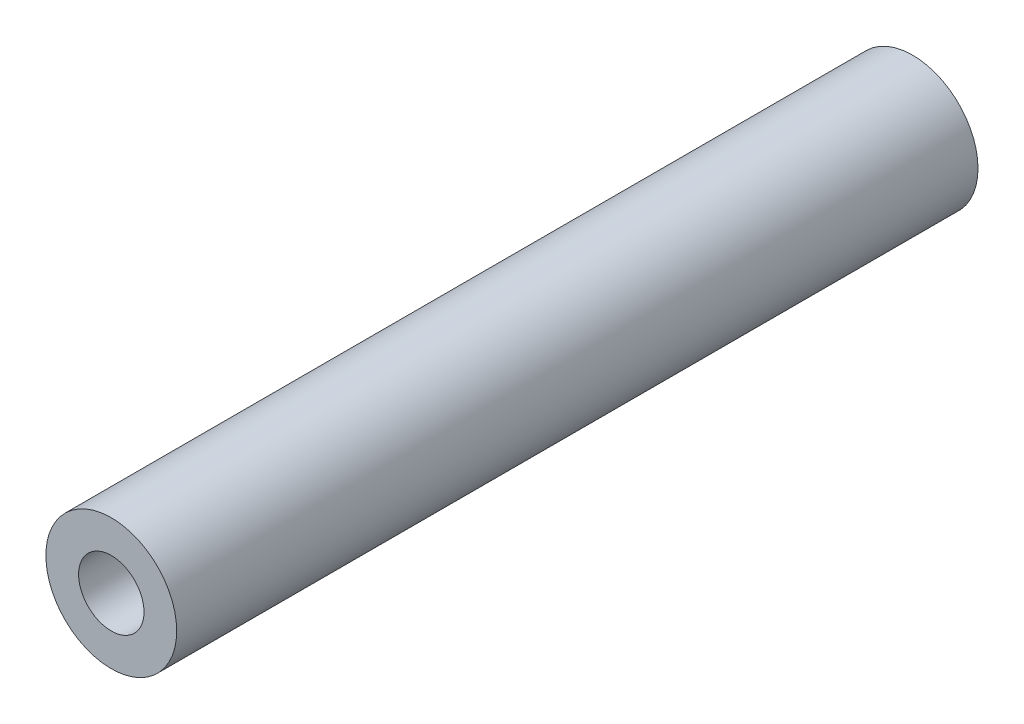
SolidWorks part; units mm, degrees
ref_plane "Plan de face" through (0, 0, 0) normal (0, 0, 1) x (1, 0, 0)
ref_plane "Plan de dessus" through (0, 0, 0) normal (0, 1, 0) x (1, 0, 0)
ref_plane "Plan de droite" through (0, 0, 0) normal (1, 0, 0) x (0, 0, -1)
sketch "Esquisse1" plane through (0, 0, 0) normal (0, 0, 1) x (1, 0, 0)
  circle A0 centre (0, 0) radius 4
extrude "Extrusion2" add sketch "Esquisse1" along normal blind 49
sketch "Esquisse2" plane through (0, 0, 49) normal (0, 0, 1) x (1, 0, 0)
  circle A0 centre (0, 0) radius 2
extrude "Extrusion3" cut sketch "Esquisse2" against normal blind 10
sketch "Esquisse3" plane through (0, 0, 0) normal (0, 0, -1) x (-1, 0, 0)
  circle A0 centre (0, 0) radius 2
extrude "Extrusion4" cut sketch "Esquisse3" against normal blind 10
